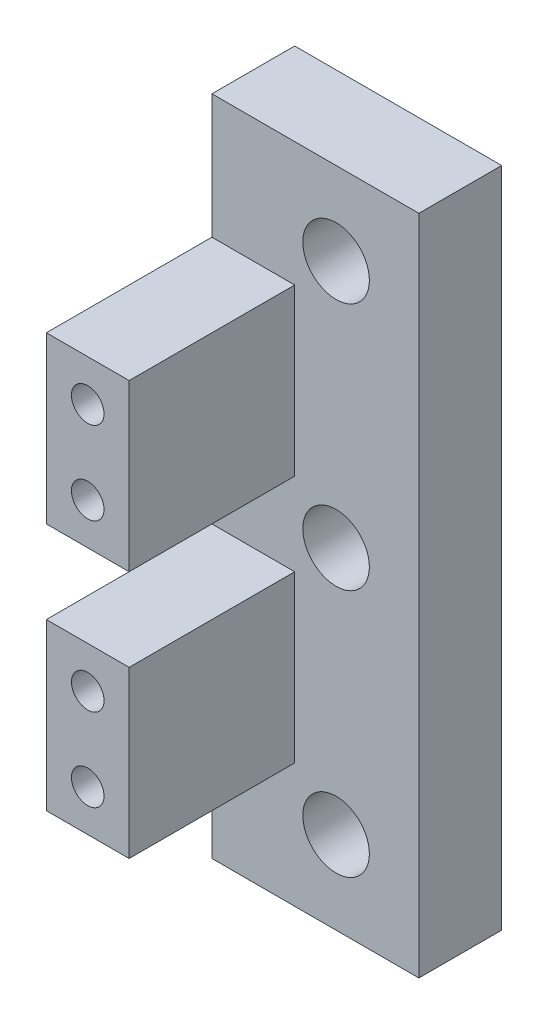
SolidWorks part; units mm, degrees
material "6061-T6 (SS)"
ref_plane "Front" through (0, 0, 0) normal (0, 0, 1) x (1, 0, 0)
ref_plane "Top" through (0, 0, 0) normal (0, 1, 0) x (1, 0, 0)
ref_plane "Right" through (0, 0, 0) normal (1, 0, 0) x (0, 0, -1)
sketch "Sketch1" plane through (0, 0, 0) normal (0, 1, 0) x (1, 0, 0)
  line L0 (0, 0) -> (0, -19.05)
  line L1 (0, -19.05) -> (6.35, -19.05)
  line L2 (6.35, -19.05) -> (6.35, -6.35)
  line L3 (6.35, -6.35) -> (15.875, -6.35)
  line L4 (15.875, -6.35) -> (15.875, 0)
  line L5 (15.875, 0) -> (0, 0)
  dimension "D1" = 6.35
  dimension "D2" = 19.05
  dimension "D3" = 15.875
  dimension "D4" = 6.35
extrude "Boss-Extrude1" add sketch "Sketch1" along normal blind 50.8
sketch "Sketch4" plane through (0, 0, 19.05) normal (0, 0, 1) x (1, 0, 0)
  line L0 (0, 0) -> (6.35, 0) construction
  line L1 (0, 0) -> (3.175, 6.35) construction
  line L2 (3.175, 6.35) -> (6.35, 0) construction
  point P0 (3.175, 6.35)
  point P16 (3.175, 12.7)
  point P17 (3.175, 19.05)
  point P18 (3.175, 25.4)
  point P19 (3.175, 31.75)
  point P20 (3.175, 38.1)
  point P21 (3.175, 44.45)
  dimension "D1" = 6.35
  dimension "D3" = 6.35
  dimension "D2" = 7
hole_wizard "M3x0.5 Tapped Hole1" positions "Sketch4" profile "Sketch3" tap size "M3x0.5" standard "ANSI Metric"
sketch "Sketch3" plane through (3.175, 38.1, 19.05) normal (1, 0, 0) x (0, -1, 0)
  line L0 (0, 0) -> (0, 8.2441)
  line L1 (0, 8.2441) -> (1.25, 7.493)
  line L2 (1.25, 7.493) -> (1.25, 0)
  line L5 (1.25, 0) -> (0, 0)
  line L10 (0, 8.2441) -> (-1.25, 7.493) construction
  line L11 (0, -6.35) -> (0, 107.95) construction
  dimension "Tap Drill Dia." = 2.5
  dimension "Tap Drill Depth" = 7.493
  dimension "Drill Angle" = 118
cosmetic thread "Hole Thread2" parameters "D1"=5.9944, "D2"=3
cosmetic thread "Hole Thread3" parameters "D1"=5.9944, "D2"=3
cosmetic thread "Hole Thread5" parameters "D1"=5.9944, "D2"=3
cosmetic thread "Hole Thread6" parameters "D1"=5.9944, "D2"=3
sketch "Sketch8" plane through (6.35, 0, 0) normal (1, 0, 0) x (0, 0, -1)
  line L0 (-19.05, 0) -> (-6.35, 0) construction
  line L10 (-19.05, 50.8) -> (-19.05, 0) construction
  line L11 (-6.35, 50.8) -> (-6.35, 0) construction
  line L12 (-6.35, 0) -> (-19.05, 0)
  line L13 (-6.35, 0) -> (-6.35, 9.525)
  line L14 (-6.35, 9.525) -> (-19.05, 9.525)
  line L15 (-19.05, 0) -> (-19.05, 9.525)
  line L16 (-6.35, 50.8) -> (-19.05, 50.8)
  line L17 (-6.35, 50.8) -> (-6.35, 41.275)
  line L18 (-6.35, 41.275) -> (-19.05, 41.275)
  line L19 (-19.05, 50.8) -> (-19.05, 41.275)
  line L20 (-6.35, 28.575) -> (-19.05, 28.575)
  line L21 (-6.35, 28.575) -> (-6.35, 22.225)
  line L22 (-6.35, 22.225) -> (-19.05, 22.225)
  line L23 (-19.05, 28.575) -> (-19.05, 22.225)
  line L24 (-6.35, 41.275) -> (-6.35, 28.575) construction
  line L25 (-6.35, 22.225) -> (-6.35, 9.525) construction
  dimension "D1" = 6.35
  dimension "D2" = 9.525
extrude "Cut-Extrude1" cut sketch "Sketch8" against normal through all
sketch "Sketch7" plane through (0, 0, 6.35) normal (0, 0, 1) x (1, 0, 0)
  line L1 (9.525, 44.45) -> (9.525, 6.35) construction
  line L3 (0, 0) -> (15.875, 0) construction
  line L4 (0, 50.8) -> (15.875, 50.8) construction
  line L6 (0, 0) -> (0, 9.525) construction
  circle A0 centre (9.525, 6.35) radius 4.7625 construction
  circle A1 centre (9.525, 25.4) radius 4.7625 construction
  point P0 (9.525, 6.35)
  point P2 (9.525, 25.4)
  point P4 (9.525, 44.45)
  dimension "D5" = 9.525
  dimension "D1" = 6.35
  dimension "D2" = 6.35
  dimension "D3" = 19.05
  dimension "D4" = 9.525
hole_wizard "#10 Clearance Hole1" positions "Sketch7" profile "Sketch6" hole size "#10" standard "ANSI Inch" end condition up to next
sketch "Sketch6" plane through (9.525, 6.35, 6.35) normal (1, 0, 0) x (0, -1, 0)
  line L0 (0, 0) -> (0, 6.35)
  line L1 (0, 6.35) -> (2.5527, 6.35)
  line L2 (2.5527, 6.35) -> (2.5527, 0)
  line L5 (2.5527, 0) -> (0, 0)
  line L11 (0, -6.35) -> (0, 107.95) construction
  dimension "Thru Hole Dia." = 5.1054
  dimension "Thru Hole Depth" = 6.35
